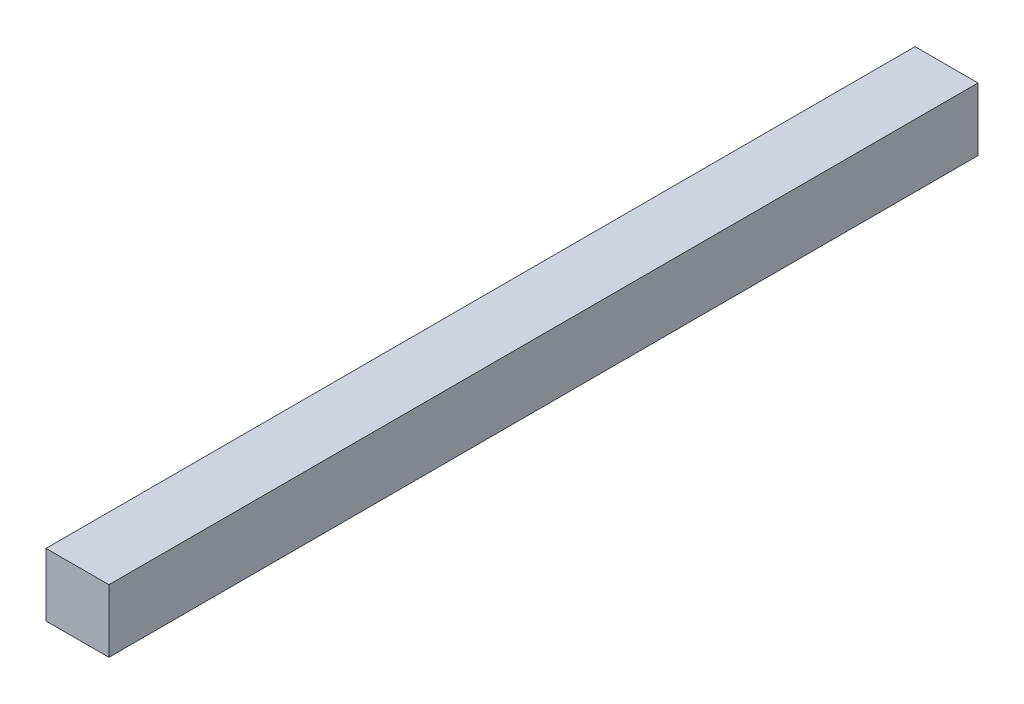
SolidWorks part; units mm, degrees
material "Pine"
ref_plane "Front Plane" through (0, 0, 0) normal (0, 0, 1) x (1, 0, 0)
ref_plane "Top Plane" through (0, 0, 0) normal (0, 1, 0) x (1, 0, 0)
ref_plane "Right Plane" through (0, 0, 0) normal (1, 0, 0) x (0, 0, -1)
sketch "Sketch1" plane through (0, 0, 0) normal (0, 0, 1) x (1, 0, 0)
  line L0 (21, 21) -> (-21, 21)
  line L1 (20, -20) -> (-20, -20)
  line L2 (20, -20) -> (20, 20)
  line L3 (20, 20) -> (-20, 20)
  line L4 (-20, -20) -> (-20, 20)
  line L5 (20, -20) -> (-20, 20) construction
  line L6 (20, 20) -> (-20, -20) construction
  line L7 (-21, -21) -> (-21, 21)
  line L8 (21, -21) -> (-21, -21)
  line L9 (21, -21) -> (21, 21)
  point P0 (0, 0)
  dimension "D1" = 40
  dimension "D2" = 40
  dimension "D3" = 1
extrude "Boss-Extrude1" add sketch "Sketch1" along normal blind 580 contours L4 L1 L2 L3 | L8 L9 L0 L7 L1 L4 L3 L2
